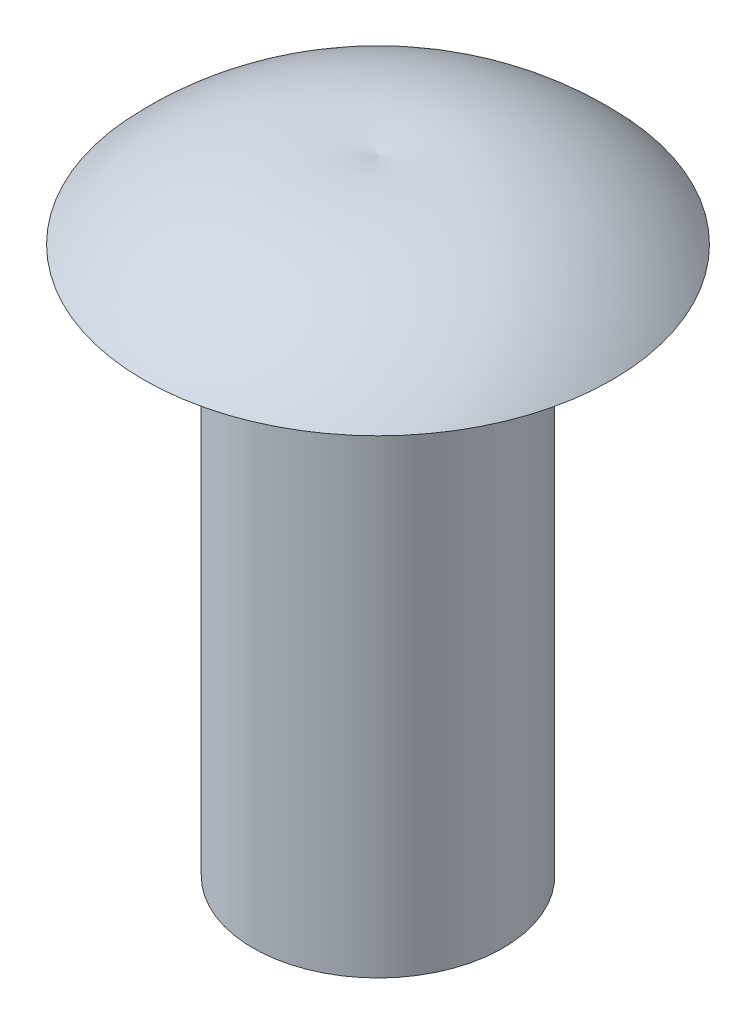
SolidWorks part; units mm, degrees
ref_plane "Front Plane" through (0, 0, 0) normal (0, 0, 1) x (1, 0, 0)
ref_plane "Top Plane" through (0, 0, 0) normal (0, 1, 0) x (1, 0, 0)
ref_plane "Right Plane" through (0, 0, 0) normal (1, 0, 0) x (0, 0, -1)
sketch "Sketch1" plane through (0, 0, 0) normal (0, 0, 1) x (1, 0, 0)
  line L0 (0, 0) -> (2.032, 0)
  line L1 (0, 0) -> (0, 10.16)
  line L2 (2.032, 0) -> (2.032, 8.89)
  line L3 (2.032, 8.89) -> (3.81, 8.89)
  arc A1 (0, 10.16) -> (3.81, 8.89) centre (0.724, 5.9821) cw
  dimension "D2" = 4.2402
  dimension "D1" = 10.16
  dimension "D3" = 8.89
  dimension "D4" = 2.032
  dimension "D5" = 0.724
revolve "Revolve1" add sketch "Sketch1" angle 360 about L1
sketch "Sketch2" plane through (0, 0, 0) normal (0, -1, 0) x (1, 0, 0)
  circle A0 centre (0, 0) radius 2.032 construction
  circle A1 centre (0, 0) radius 2.032
scale "Scale1" scale about centroid uniform scaling yes scale factor 1.21
